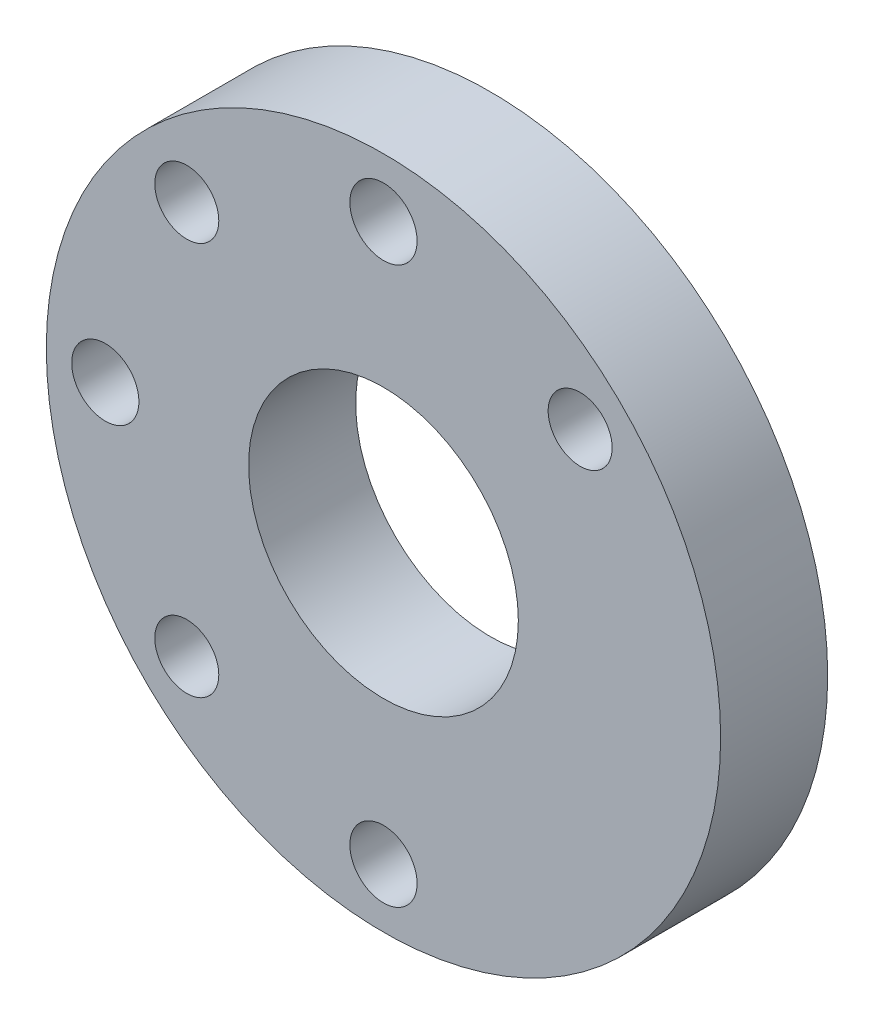
SolidWorks part; units mm, degrees
material "Balsa"
ref_plane "Front Plane" through (0, 0, 0) normal (0, 0, 1) x (1, 0, 0)
ref_plane "Top Plane" through (0, 0, 0) normal (0, 1, 0) x (1, 0, 0)
ref_plane "Right Plane" through (0, 0, 0) normal (1, 0, 0) x (0, 0, -1)
sketch "Sketch1" plane through (0, 0, 0) normal (0, 0, 1) x (1, 0, 0)
  circle A1 centre (0, 0) radius 8
  circle A2 centre (0, 0) radius 16.5 construction
  circle A3 centre (0, 16.5) radius 1.9939
  circle A4 centre (11.6673, 11.6673) radius 1.8986
  circle A5 centre (16.5, 0) radius 1.9939 construction
  circle A6 centre (11.6673, -11.6673) radius 1.8986 construction
  circle A7 centre (0, -16.5) radius 1.9939
  circle A8 centre (-11.6673, -11.6673) radius 1.8986
  circle A9 centre (-16.5, 0) radius 1.9939
  circle A10 centre (-11.6673, 11.6673) radius 1.8986
  circle A11 centre (0, 0) radius 20
  dimension "D1" = 40
  dimension "D2" = 16
  dimension "D3" = 33
  dimension "D4" = 3.9878
  dimension "D5" = 3.7973
  dimension "D6" = 45
  dimension "D7" = 4
extrude "Boss-Extrude1" add sketch "Sketch1" along normal blind 6.35
other "Move Face1" [suppressed] parameters "D1"=0.08
